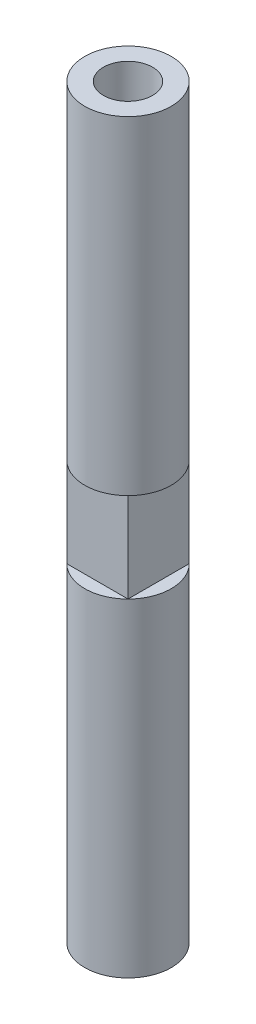
SolidWorks part; units mm, degrees
material "6061-T6 (SS)"
ref_plane "Front Plane" through (0, 0, 0) normal (0, 0, 1) x (1, 0, 0)
ref_plane "Top Plane" through (0, 0, 0) normal (0, 1, 0) x (1, 0, 0)
ref_plane "Right Plane" through (0, 0, 0) normal (1, 0, 0) x (0, 0, -1)
sketch "Sketch1" plane through (0, 0, 0) normal (0, 1, 0) x (1, 0, 0)
  line L1 (-3.683, -3.683) -> (3.683, -3.683) construction
  line L2 (-3.683, -3.683) -> (-3.683, 3.683) construction
  line L3 (-3.683, 3.683) -> (3.683, 3.683) construction
  line L4 (3.683, -3.683) -> (3.683, 3.683) construction
  line L5 (-3.683, -3.683) -> (3.683, 3.683) construction
  line L6 (-3.683, 3.683) -> (3.683, -3.683) construction
  circle A0 centre (0, 0) radius 3.683
  dimension "D1" = 7.366
extrude "Boss-Extrude1" add sketch "Sketch1" along normal blind 63.5
hole_wizard "Tap Drill for M5x0.8 Tap1" [suppressed] positions "Sketch3" profile "Sketch4" hole size "M5x0.8" standard "ANSI Metric"
sketch "Sketch3" plane through (0, 63.5, 0) normal (0, 1, 0) x (1, 0, 0)
  point P0 (0, 0)
sketch "Sketch4" plane through (0, 63.5, 0) normal (1, 0, 0) x (0, 0, 1)
  line L0 (0, 0) -> (0, 26.2618)
  line L1 (0, 26.2618) -> (2.1, 25)
  line L2 (2.1, 25) -> (2.1, 0)
  line L5 (2.1, 0) -> (0, 0)
  line L10 (0, 26.2618) -> (-2.1, 25) construction
  line L11 (0, -6.35) -> (0, 107.95) construction
  dimension "Hole Dia." = 4.2
  dimension "Hole Depth" = 25
  dimension "Drill Angle" = 118
hole_wizard "Tap Drill for M5x0.8 Tap2" [suppressed] positions "Sketch5" profile "Sketch6" hole size "M5x0.8" standard "ANSI Metric"
sketch "Sketch5" plane through (0, 0, 0) normal (0, -1, 0) x (-1, 0, 0)
  point P0 (0, 0)
sketch "Sketch6" plane through (0, 0, 0) normal (1, 0, 0) x (0, 0, -1)
  line L0 (0, 0) -> (0, 26.1538)
  line L1 (0, 26.1538) -> (2.1, 24.892)
  line L2 (2.1, 24.892) -> (2.1, 0)
  line L5 (2.1, 0) -> (0, 0)
  line L10 (0, 26.1538) -> (-2.1, 24.892) construction
  line L11 (0, -6.35) -> (0, 107.95) construction
  dimension "Hole Dia." = 4.2
  dimension "Hole Depth" = 24.892
  dimension "Drill Angle" = 118
sketch "Sketch7" plane through (0, 0, 0) normal (0, -1, 0) x (1, 0, 0)
  circle A0 centre (0, 0) radius 2.09
  dimension "D1" = 4.18
extrude "Cut-Extrude1" cut sketch "Sketch7" against normal blind 20.32
ref_plane "Plane1" through (0, 31.75, 0) normal (0, -1, 0) x (-1, 0, 0)
mirror "Mirror1" about plane through (0, 31.75, 0) normal (0, -1, 0) of "Cut-Extrude1"
fillet "Fillet1" [suppressed] radius 1.27
sketch "Sketch8" plane through (0, 31.75, 0) normal (0, -1, 0) x (-1, 0, 0)
  line L1 (-2.6043, -2.6043) -> (2.6043, -2.6043)
  line L2 (-2.6043, -2.6043) -> (-2.6043, 2.6043)
  line L3 (-2.6043, 2.6043) -> (2.6043, 2.6043)
  line L4 (2.6043, -2.6043) -> (2.6043, 2.6043)
  line L5 (-2.6043, -2.6043) -> (2.6043, 2.6043) construction
  line L6 (-2.6043, 2.6043) -> (2.6043, -2.6043) construction
  circle A0 centre (0, 0) radius 3.683 construction
  point P0 (0, 0)
extrude "Cut-Extrude3" cut sketch "Sketch8" against normal mid plane 7.62 flip side to cut
